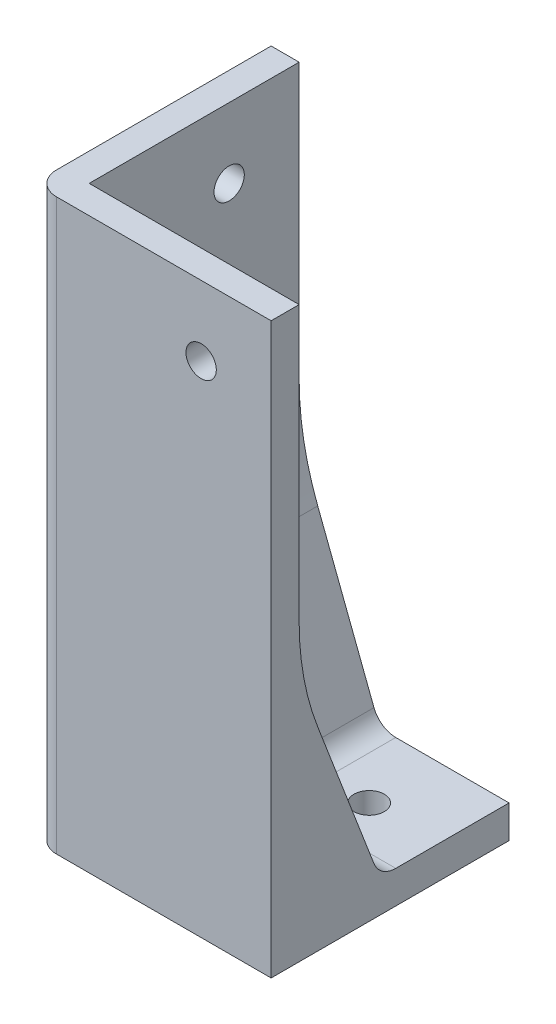
SolidWorks part; units mm, degrees
material "ABS PC"
ref_plane "Front Plane" through (0, 0, 0) normal (0, 0, 1) x (1, 0, 0)
ref_plane "Top Plane" through (0, 0, 0) normal (0, 1, 0) x (1, 0, 0)
ref_plane "Right Plane" through (0, 0, 0) normal (1, 0, 0) x (0, 0, -1)
sketch "Sketch2" plane through (0, 0, 0) normal (0, 1, 0) x (1, 0, 0)
  line L0 (0, 0) -> (0, 51)
  line L1 (0, 0) -> (51, 0)
  line L2 (0, 51) -> (51, 51)
  line L3 (51, 0) -> (51, 51)
  circle A0 centre (36, 36) radius 3.25
  dimension "D2" = 6.5
  dimension "D3" = 15
  dimension "D4" = 15
  dimension "D1" = 51
extrude "Boss-Extrude2" add sketch "Sketch2" along normal blind 7
sketch "Sketch3" plane through (0, 7, 0) normal (0, 1, 0) x (1, 0, 0)
  line L0 (51, 0) -> (0, 0)
  line L1 (0, 0) -> (0, 51)
  line L2 (0, 51) -> (6, 51)
  line L3 (51, 51) -> (0, 51) construction
  line L4 (6, 51) -> (6, 6)
  line L5 (6, 6) -> (51, 6)
  line L6 (51, 0) -> (51, 51) construction
  line L7 (51, 6) -> (51, 0)
  dimension "D1" = 6
extrude "Boss-Extrude3" add sketch "Sketch3" along normal blind 115
hole_wizard "Ø6.5 (6.5) Diameter Hole1" positions "Sketch5" profile "Sketch4" hole size "Ø6.5" standard "ANSI Metric"
sketch "Sketch5" plane through (0, 0, 0) normal (0, 0, 1) x (1, 0, 0)
  line L0 (0, 122) -> (51, 122) construction
  line L1 (51, 122) -> (51, 0) construction
  point P1 (36, 107)
  dimension "D1" = 15
  dimension "D2" = 15
sketch "Sketch4" plane through (36, 107, 0) normal (1, 0, 0) x (0, -1, 0)
  line L0 (0, 0) -> (0, 7.9528)
  line L1 (0, 7.9528) -> (3.25, 6)
  line L2 (3.25, 6) -> (3.25, 0)
  line L5 (3.25, 0) -> (0, 0)
  line L10 (0, 7.9528) -> (-3.25, 6) construction
  line L11 (0, -6.35) -> (0, 107.95) construction
  dimension "Hole Dia." = 6.5
  dimension "Hole Depth" = 6
  dimension "Drill Angle" = 118
hole_wizard "Ø6.5 (6.5) Diameter Hole2" positions "Sketch7" profile "Sketch6" hole size "Ø6.5" standard "ANSI Metric"
sketch "Sketch7" plane through (0, 0, 0) normal (-1, 0, 0) x (0, 0, 1)
  line L0 (-51, 122) -> (0, 122) construction
  line L1 (-51, 122) -> (-51, 0) construction
  point P0 (-36, 107)
  dimension "D1" = 15
  dimension "D2" = 15
sketch "Sketch6" plane through (0, 107, -36) normal (0, 1, 0) x (0, 0, 1)
  line L0 (0, 0) -> (0, 7.9528)
  line L1 (0, 7.9528) -> (3.25, 6)
  line L2 (3.25, 6) -> (3.25, 0)
  line L5 (3.25, 0) -> (0, 0)
  line L10 (0, 7.9528) -> (-3.25, 6) construction
  line L11 (0, -6.35) -> (0, 107.95) construction
  dimension "Hole Dia." = 6.5
  dimension "Hole Depth" = 6
  dimension "Drill Angle" = 118
chamfer "Chamfer1" distance 45 angle 21 2 edges
fillet "Fillet1" radius 5 1 edges at (0, 61, 0)
fillet "Fillet2" radius 60 2 edges at (28.5, 52, -6) (6, 52, -28.5)
fillet "Fillet3" radius 5 2 edges at (23.2739, 7, -37.1369) (37.1369, 7, -23.2739)
